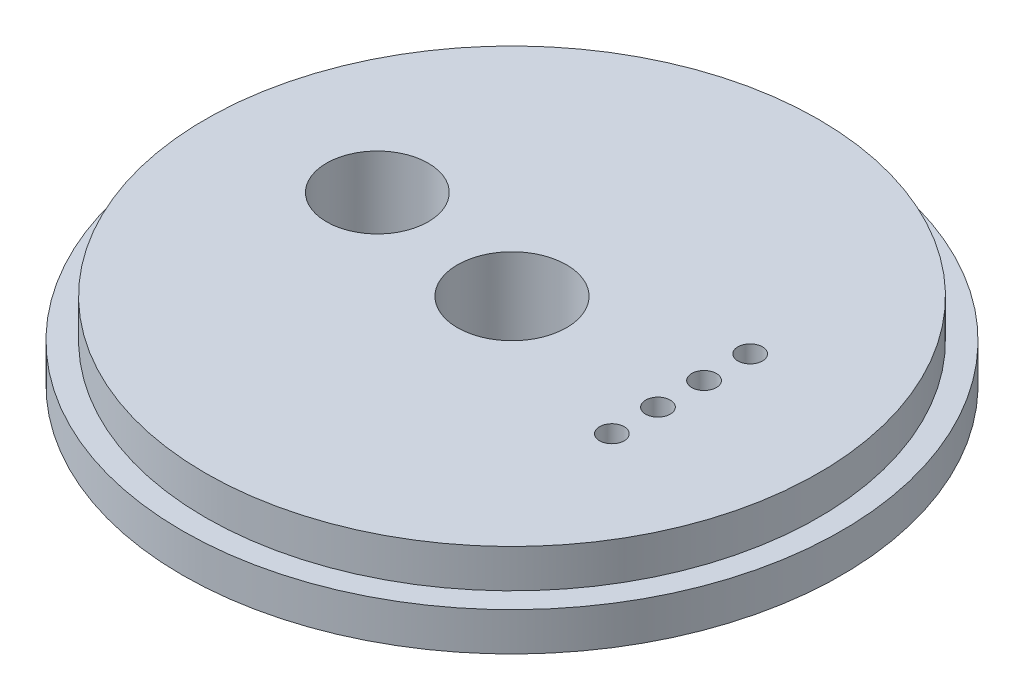
SolidWorks part; units mm, degrees
ref_plane "Front Plane" through (0, 0, 0) normal (0, 0, 1) x (1, 0, 0)
ref_plane "Top Plane" through (0, 0, 0) normal (0, 1, 0) x (1, 0, 0)
ref_plane "Right Plane" through (0, 0, 0) normal (1, 0, 0) x (0, 0, -1)
sketch "Sketch1" plane through (0, 0, 0) normal (0, 1, 0) x (1, 0, 0)
  circle A0 centre (0, 0) radius 27.2415
  dimension "D1" = 54.483
extrude "Boss-Extrude1" add sketch "Sketch1" along normal blind 3.175
sketch "Sketch2" plane through (0, 3.175, 0) normal (0, 1, 0) x (1, 0, 0)
  circle A0 centre (0, 0) radius 25.3365
  dimension "D1" = 50.673
extrude "Boss-Extrude2" add sketch "Sketch2" along normal blind 3.175
sketch "Sketch5" plane through (0, 0, 0) normal (0, -1, 0) x (1, 0, 0)
  circle A2 centre (-12.9926, -1.863) radius 4.2037
  dimension "D1" = 8.4074
extrude "Cut-Extrude1" cut sketch "Sketch5" against normal up to surface (6.35 mm away) up to face at (0, 6.35, 25.3365)
sketch "Sketch6" plane through (0, 0, 0) normal (0, -1, 0) x (1, 0, 0)
  circle A0 centre (0, 0) radius 4.5085
  dimension "D1" = 9.017
extrude "Cut-Extrude2" cut sketch "Sketch6" against normal up to next
sketch "Sketch9" plane through (0, 6.35, 0) normal (0, 1, 0) x (1, 0, 0)
  line L0 (13.97, 5.715) -> (13.97, 1.905) construction
  line L1 (13.97, 1.905) -> (13.97, -1.905) construction
  line L2 (13.97, -1.905) -> (13.97, -5.715) construction
  circle A0 centre (13.97, 5.715) radius 1.016
  circle A1 centre (13.97, 1.905) radius 1.016
  circle A2 centre (13.97, -1.905) radius 1.016
  circle A3 centre (13.97, -5.715) radius 1.016
  point P8 (13.97, 0)
  dimension "D2" = 2.032
  dimension "D1" = 3.81
  dimension "D3" = 13.97
extrude "Cut-Extrude3" cut sketch "Sketch9" against normal up to next
